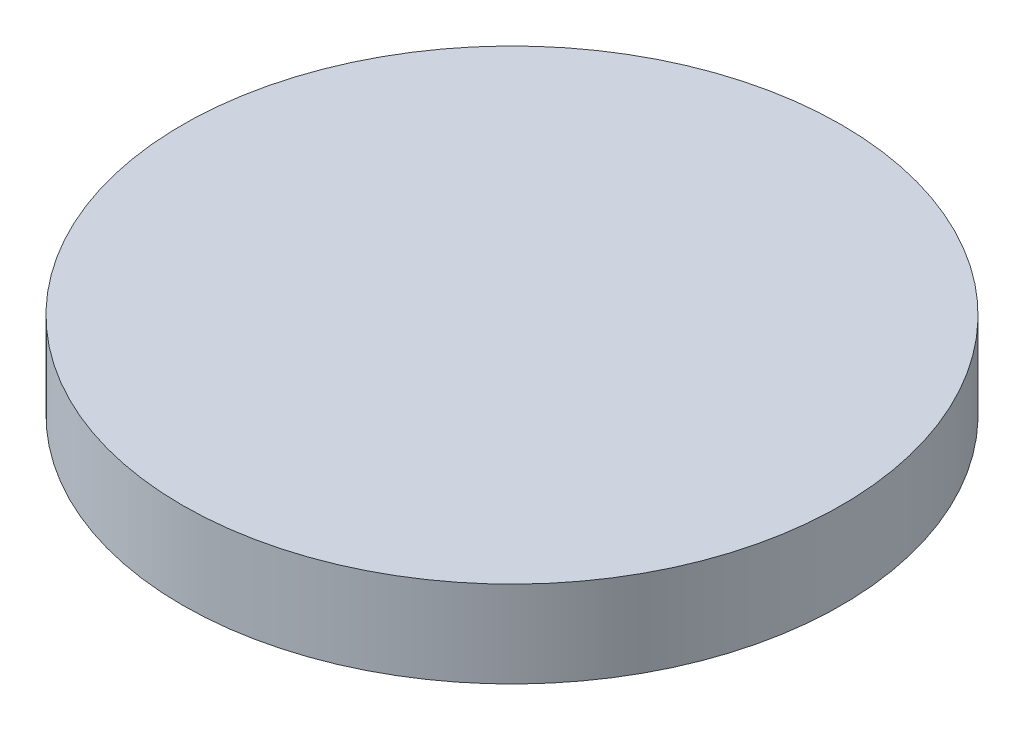
SolidWorks part; units mm, degrees
ref_plane "Front Plane" through (0, 0, 0) normal (0, 0, 1) x (1, 0, 0)
ref_plane "Top Plane" through (0, 0, 0) normal (0, 1, 0) x (1, 0, 0)
ref_plane "Right Plane" through (0, 0, 0) normal (1, 0, 0) x (0, 0, -1)
sketch "Sketch1" plane through (0, 0, 0) normal (0, 1, 0) x (1, 0, 0)
  circle A0 centre (0, 0) radius 76.2
  dimension "D1" = 152.4
extrude "Boss-Extrude1" add sketch "Sketch1" along normal blind 20 contours A0
